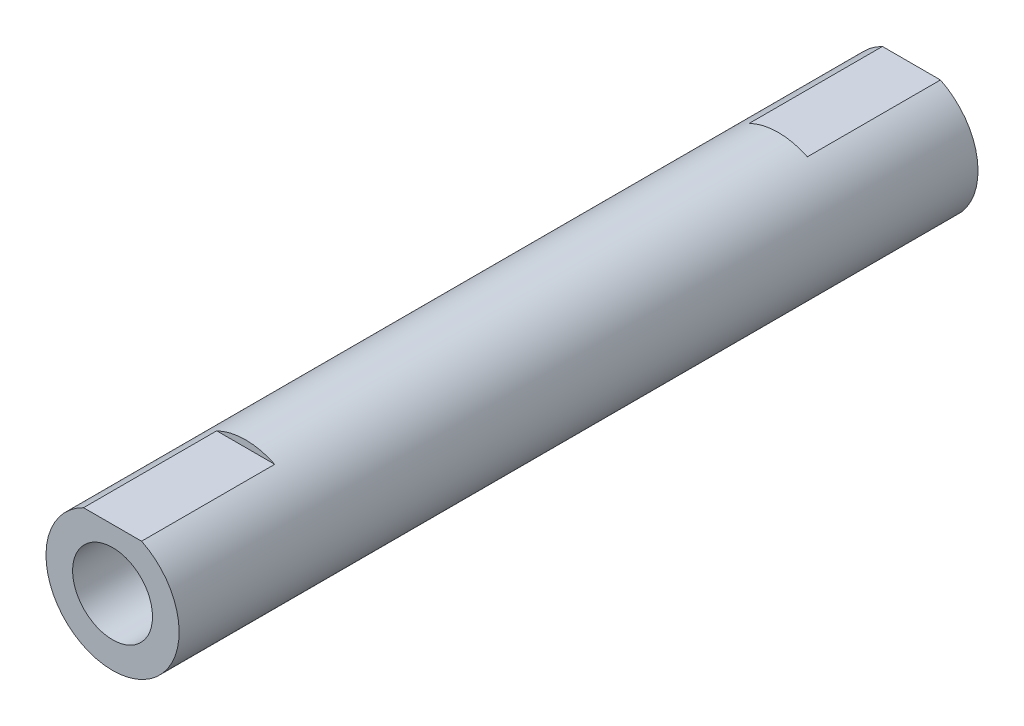
SolidWorks part; units mm, degrees
ref_plane "Front Plane" through (0, 0, 0) normal (0, 0, 1) x (1, 0, 0)
ref_plane "Top Plane" through (0, 0, 0) normal (0, 1, 0) x (1, 0, 0)
ref_plane "Right Plane" through (0, 0, 0) normal (1, 0, 0) x (0, 0, -1)
sketch "Sketch1" plane through (0, 0, 0) normal (0, 0, 1) x (1, 0, 0)
  circle A0 centre (0, 0) radius 3
  circle A1 centre (0, 0) radius 5
  dimension "D1" = 6
  dimension "D2" = 10
extrude "Boss-Extrude2" add sketch "Sketch1" along normal mid plane 60
sketch "Sketch2" plane through (0, 0, 30) normal (0, 0, 1) x (1, 0, 0)
  line L0 (2.1794, 4.5) -> (-2.1794, 4.5)
  circle A0 centre (0, 0) radius 5 construction
  arc A1 (2.1794, 4.5) -> (-2.1794, 4.5) centre (0, 0) ccw
  dimension "D1" = 4.5
extrude "Cut-Extrude1" cut sketch "Sketch2" against normal blind 10 contours A1 L0
mirror "Mirror1" about plane through (0, 0, 0) normal (0, 0, 1) of "Cut-Extrude1"
